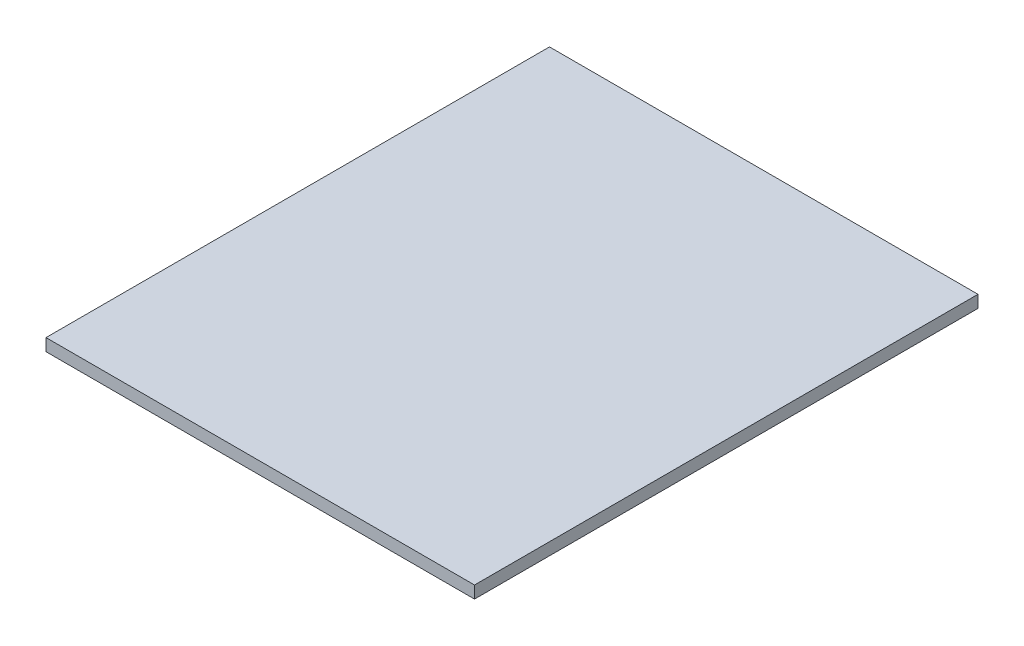
SolidWorks part; units mm, degrees
ref_plane "Front Plane" through (0, 0, 0) normal (0, 0, 1) x (1, 0, 0)
ref_plane "Top Plane" through (0, 0, 0) normal (0, 1, 0) x (1, 0, 0)
ref_plane "Right Plane" through (0, 0, 0) normal (1, 0, 0) x (0, 0, -1)
sketch "Sketch1" plane through (0, 0, 0) normal (0, 1, 0) x (1, 0, 0)
  line L1 (0, 0) -> (560, 0)
  line L2 (0, 0) -> (0, 658)
  line L3 (0, 658) -> (560, 658)
  line L4 (560, 0) -> (560, 658)
  dimension "D1" = 658
  dimension "D2" = 560
extrude "Extrude1" add sketch "Sketch1" along normal blind 16
